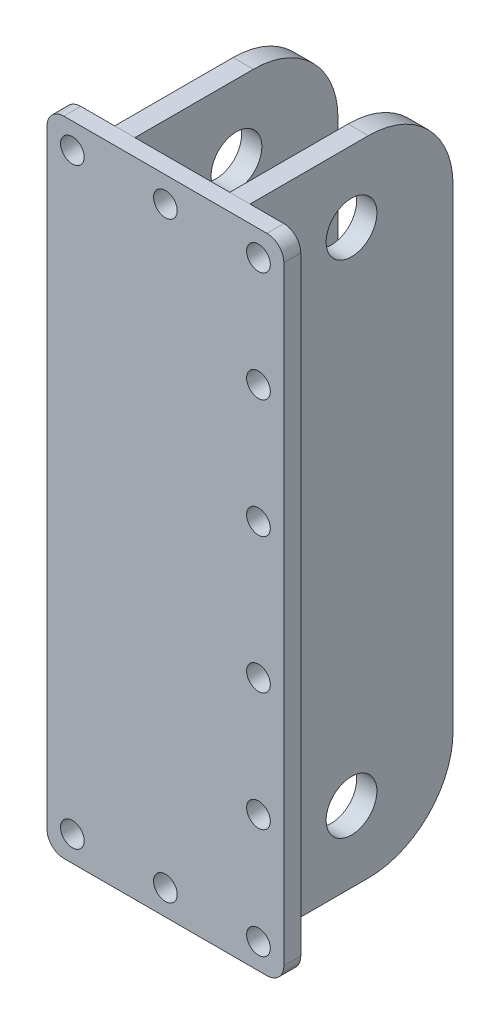
SolidWorks part; units mm, degrees
material "普通碳钢"
ref_plane "前视基准面" through (0, 0, 0) normal (0, 0, 1) x (1, 0, 0)
ref_plane "上视基准面" through (0, 0, 0) normal (0, 1, 0) x (1, 0, 0)
ref_plane "右视基准面" through (0, 0, 0) normal (1, 0, 0) x (0, 0, -1)
sketch "草图1" plane through (0, 0, 0) normal (0, 0, 1) x (1, 0, 0)
  line L1 (10, 0) -> (130, 0)
  line L2 (0, 10) -> (0, 370)
  line L3 (10, 380) -> (130, 380)
  line L4 (140, 10) -> (140, 370)
  arc A0 (130, 0) -> (140, 10) centre (130, 10) ccw
  arc A1 (10, 0) -> (0, 10) centre (10, 10) cw
  arc A2 (130, 380) -> (140, 370) centre (130, 370) cw
  arc A3 (0, 370) -> (10, 380) centre (10, 370) cw
  point P10 (0, 0)
  point P13 (140, 380)
  point P16 (0, 380)
  dimension "D3" = 10
  dimension "D1" = 380
  dimension "D2" = 140
extrude "凸台-拉伸1" add sketch "草图1" along normal blind 10
sketch "草图2" plane through (0, 0, 10) normal (0, 0, 1) x (1, 0, 0)
  line L0 (0, 365) -> (140, 365) construction
  line L1 (0, 370) -> (0, 10) construction
  line L2 (140, 10) -> (140, 370) construction
  line L3 (15, 380) -> (15, 0) construction
  line L4 (130, 380) -> (10, 380) construction
  line L5 (10, 0) -> (130, 0) construction
  line L6 (125, 380) -> (125, 0) construction
  line L7 (0, 15) -> (140, 15) construction
  line L8 (0, 300) -> (140, 300) construction
  line L9 (0, 80) -> (140, 80) construction
  line L10 (0, 230) -> (140, 230) construction
  line L11 (0, 150) -> (140, 150) construction
  circle A0 centre (15, 365) radius 7
  circle A1 centre (125, 365) radius 7
  circle A2 centre (15, 15) radius 7
  circle A3 centre (125, 15) radius 7
  circle A4 centre (70, 365) radius 7
  circle A5 centre (70, 15) radius 7
  circle A8 centre (125, 300) radius 7
  circle A12 centre (125, 80) radius 7
  circle A13 centre (125, 230) radius 7
  circle A14 centre (125, 150) radius 7
  dimension "D1" = 15
  dimension "D5" = 65
  dimension "D9" = 14
  dimension "D2" = 15
  dimension "D3" = 15
  dimension "D4" = 15
  dimension "D6" = 65
  dimension "D7" = 70
  dimension "D8" = 70
extrude "切除-拉伸1" cut sketch "草图2" against normal up to next
sketch "草图3" plane through (0, 0, 0) normal (0, 0, -1) x (-1, 0, 0)
  line L0 (-130, 380) -> (-10, 380) construction
  line L1 (-110, 380) -> (-98, 380)
  line L2 (-110, 380) -> (-110, 0)
  line L3 (-110, 0) -> (-98, 0)
  line L4 (-98, 380) -> (-98, 0)
  line L5 (-10, 0) -> (-130, 0) construction
  line L6 (-42, 380) -> (-30, 380)
  line L7 (-42, 380) -> (-42, 0)
  line L8 (-42, 0) -> (-30, 0)
  line L9 (-30, 380) -> (-30, 0)
  line L10 (-140, 10) -> (-140, 370) construction
  line L11 (0, 370) -> (0, 10) construction
  dimension "D1" = 12
  dimension "D2" = 12
  dimension "D3" = 30
  dimension "D4" = 30
extrude "凸台-拉伸2" add sketch "草图3" along normal blind 120 separate body
fillet "圆角1" radius 50 2 edges at (104, 380, -120) (104, 0, -120)
fillet "圆角2" radius 50 2 edges at (36, 0, -120) (36, 380, -120)
sketch "草图4" plane through (110, 0, 0) normal (1, 0, 0) x (0, 0, -1)
  line L0 (60, 338) -> (60, 42) construction
  line L1 (70, 380) -> (0, 380) construction
  line L3 (70, 0) -> (0, 0) construction
  line L4 (120, 330) -> (120, 50) construction
  circle A0 centre (60, 338) radius 15
  circle A1 centre (60, 42) radius 15
  dimension "D1" = 42
  dimension "D3" = 30
  dimension "D4" = 30
  dimension "D2" = 60
  dimension "D5" = 42
extrude "切除-拉伸2" cut sketch "草图4" against normal up to next (12 mm away)
sketch "草图5" plane through (30, 0, 0) normal (-1, 0, 0) x (0, 0, 1)
  line L0 (-60, 338) -> (-60, 42) construction
  line L1 (-70, 380) -> (0, 380) construction
  line L2 (-70, 0) -> (0, 0) construction
  line L4 (-120, 50) -> (-120, 330) construction
  circle A0 centre (-60, 338) radius 15
  circle A1 centre (-60, 42) radius 15
  dimension "D1" = 42
  dimension "D4" = 30
  dimension "D5" = 30
  dimension "D2" = 42
  dimension "D3" = 60
extrude "切除-拉伸3" cut sketch "草图5" against normal up to next (12 mm away)
